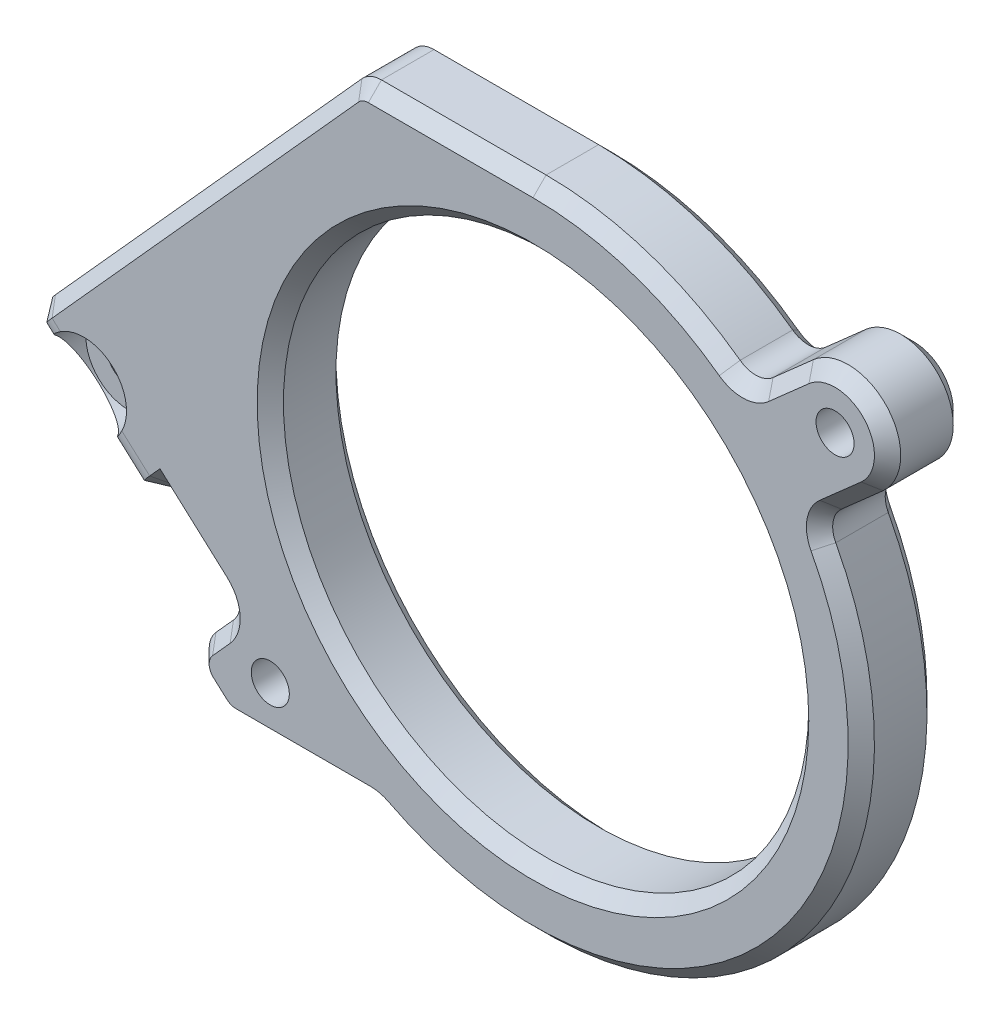
SolidWorks part; units mm, degrees
ref_plane "正面" through (0, 0, 0) normal (0, 0, 1) x (1, 0, 0)
ref_plane "平面" through (0, 0, 0) normal (0, 1, 0) x (1, 0, 0)
ref_plane "右側面" through (0, 0, 0) normal (1, 0, 0) x (0, 0, -1)
sketch "ｽｹｯﾁ1" plane through (0, 0, 0) normal (0, 0, 1) x (1, 0, 0)
  line L1 (30, -27.5) -> (-30, -27.5)
  line L2 (30, -27.5) -> (30, 27.5)
  line L3 (30, 27.5) -> (-30, 27.5)
  line L4 (-30, -27.5) -> (-30, 27.5)
  line L5 (30, -27.5) -> (-30, 27.5) construction
  line L6 (30, 27.5) -> (-30, -27.5) construction
  point P0 (0, 0)
  dimension "D1" = 55
  dimension "D2" = 60
extrude "ﾎﾞｽ - 押し出し1" add sketch "ｽｹｯﾁ1" along normal blind 6
sketch "ｽｹｯﾁ2" plane through (0, 0, 6) normal (0, 0, 1) x (1, 0, 0)
  line L0 (23, 20) -> (-20, -18)
  point P2 (0, 0)
  dimension "D1" = 18
  dimension "D2" = 20
  dimension "D3" = 43
  dimension "D4" = 38
hole_wizard "M4 すきま穴1" positions "ｽｹｯﾁ3" profile "ｽｹｯﾁ4" hole size "M4" standard "ISO"
sketch "ｽｹｯﾁ3" plane through (0, 0, 6) normal (0, 0, 1) x (1, 0, 0)
  point P0 (-20, -18)
  point P3 (23, 20)
sketch "ｽｹｯﾁ4" plane through (-20, -18, 6) normal (1, 0, 0) x (0, -1, 0)
  line L0 (0, 0) -> (0, 10)
  line L1 (0, 10) -> (1.45, 10)
  line L2 (1.45, 10) -> (1.45, 0)
  line L5 (1.45, 0) -> (0, 0)
  line L10 (0, 10) -> (-1.45, 10) construction
  line L11 (0, -6.35) -> (0, 107.95) construction
  dimension "穴の直径" = 2.9
  dimension "穴の深さ" = 10
  dimension "ﾄﾞﾘﾙ角度" = 180
sketch "ｽｹｯﾁ5" plane through (0, 0, 6) normal (0, 0, 1) x (1, 0, 0)
  circle A0 centre (0, 0) radius 20
  dimension "D1" = 40
extrude "ｶｯﾄ - 押し出し1" cut sketch "ｽｹｯﾁ5" against normal through all
sketch "ｽｹｯﾁ6" plane through (0, 0, 6) normal (0, 0, 1) x (1, 0, 0)
  line L0 (-20, -18) -> (23, 20) construction
  line L1 (23, 20) -> (-20, -18) construction
  line L2 (-22.6488, -15.0027) -> (20.3512, 22.9973)
  line L3 (-17.3512, -20.9973) -> (25.6488, 17.0027)
  line L8 (-30, 27.5) -> (-30, -27.5)
  line L9 (-30, -27.5) -> (30, -27.5)
  line L10 (30, -27.5) -> (30, 27.5)
  line L11 (30, 27.5) -> (-30, 27.5)
  line L12 (-30, 27.5) -> (-30, -27.5)
  line L13 (-30, -27.5) -> (30, -27.5)
  line L14 (30, -27.5) -> (30, 27.5)
  line L15 (30, 27.5) -> (-30, 27.5)
  circle A0 centre (0, 0) radius 20 construction
  circle A1 centre (0, 0) radius 20
  arc A2 (-22.6488, -15.0027) -> (-17.3512, -20.9973) centre (-20, -18) ccw
  arc A3 (25.6488, 17.0027) -> (20.3512, 22.9973) centre (23, 20) ccw
  circle A4 centre (0, 0) radius 25
  point P8 (1.5, 1)
  dimension "D2" = 50
  dimension "D1" = 8
  dimension "D3" = 0
extrude "ｶｯﾄ - 押し出し2" cut sketch "ｽｹｯﾁ6" against normal through all contours L13 L14 L15 L12 | A4 | A2 L3 A3 L2
sketch "ｽｹｯﾁ7" plane through (0, 0, 6) normal (0, 0, 1) x (1, 0, 0)
  line L0 (0, 25) -> (-20, 25)
  line L1 (-20, -22) -> (-21.5, -22)
  line L2 (-20, -22) -> (-20, 25)
  line L3 (-20, 25) -> (-21.5, 25)
  line L4 (-21.5, -22) -> (-21.5, 25)
  line L5 (-20, -22) -> (-11.8743, -22)
  line L8 (-21.0078, -13.5525) -> (-22.6488, -15.0027)
  line L9 (-17.3512, -20.9973) -> (-15.651, -19.4948)
  line L10 (21.2717, 13.1345) -> (25.6488, 17.0027)
  line L11 (20.3512, 22.9973) -> (16.0334, 19.1815)
  line L12 (-21.0078, -13.5525) -> (-22.6488, -15.0027)
  line L13 (-17.3512, -20.9973) -> (-15.651, -19.4948)
  line L14 (21.2717, 13.1345) -> (25.6488, 17.0027)
  line L15 (20.3512, 22.9973) -> (16.0334, 19.1815)
  arc A0 (-22.6488, -15.0027) -> (-17.3512, -20.9973) centre (-20, -18) ccw construction
  arc A5 (-22.6488, -15.0027) -> (-17.3512, -20.9973) centre (-20, -18) ccw
  arc A6 (-15.651, -19.4948) -> (21.2717, 13.1345) centre (0, 0) ccw
  arc A7 (25.6488, 17.0027) -> (20.3512, 22.9973) centre (23, 20) ccw
  arc A8 (16.0334, 19.1815) -> (-21.0078, -13.5525) centre (0, 0) ccw
  arc A9 (-22.6488, -15.0027) -> (-17.3512, -20.9973) centre (-20, -18) ccw
  arc A10 (-15.651, -19.4948) -> (21.2717, 13.1345) centre (0, 0) ccw
  arc A11 (25.6488, 17.0027) -> (20.3512, 22.9973) centre (23, 20) ccw
  arc A12 (16.0334, 19.1815) -> (-21.0078, -13.5525) centre (0, 0) ccw
  line M17 (-21.0078, -13.5525) -> (-22.6488, -15.0027)
  arc M18 (-22.6488, -15.0027) -> (-17.3512, -20.9973) centre (-20, -18) ccw
  line M19 (-17.3512, -20.9973) -> (-15.651, -19.4948)
  arc M20 (-15.651, -19.4948) -> (21.2717, 13.1345) centre (0, 0) ccw
  arc M24 (16.0334, 19.1815) -> (-21.0078, -13.5525) centre (0, 0) ccw
  dimension "D2" = 1.5
  dimension "D1" = 0
extrude "ﾎﾞｽ - 押し出し2" add sketch "ｽｹｯﾁ7" against normal up to surface (6 mm away) contours L4 L1 M18 M17 M24 | L4 L2 L3 M24 | L2 L0 M24 | L5 M18 M20 M19
sketch "ｽｹｯﾁ8" plane through (0, 0, 6) normal (0, 0, 1) x (1, 0, 0)
  line L0 (-21.5, 25) -> (-45.7174, -1.8961)
  line L1 (-45.7174, -1.8961) -> (-23.3898, -22)
  line L3 (-21.5, 12.7574) -> (-21.5, 25) construction
  line L4 (-20, -22) -> (-23.3898, -22)
  point P3 (-22.5, -21)
  point P9 (-21.5, -22)
  point P10 (0, 0)
  point P11 (0, 0)
  point P13 (0, 0)
  point P15 (-21.5, -22)
  point P16 (-24.0724, -22)
  point P17 (-21.5, 25)
  point P19 (0, 0)
  point P20 (-21.6569, -22)
  point P21 (0, 0)
  dimension "D1" = 42
  dimension "D2" = 32
extrude "ﾎﾞｽ - 押し出し3" add sketch "ｽｹｯﾁ8" against normal up to surface (6 mm away) up to face at (-3.845, 3.3122, 0)
sketch "ｽｹｯﾁ9" plane through (0, 0, 0) normal (0, 0, -1) x (-1, 0, 0)
  line L0 (32.3408, -13.9405) -> (25.6495, -6.509)
  line L1 (23.3898, -22) -> (45.7174, -1.8961) construction
  line L2 (25.6495, -6.509) -> (39.0261, 5.5353)
  line L3 (45.7174, -1.8961) -> (21.5, 25) construction
  line M4 (23.3898, -22) -> (45.7174, -1.8961)
  line M5 (45.7174, -1.8961) -> (21.5, 25)
  dimension "D1" = 10
  dimension "D2" = 18
extrude "ﾎﾞｽ - 押し出し4" add sketch "ｽｹｯﾁ9" along normal blind 4 contours L2 L0 M4 M5
sketch "ｽｹｯﾁ10" plane through (0, 0, -4) normal (0, 0, -1) x (-1, 0, 0)
  line L0 (32.3408, -13.9405) -> (25.6495, -6.509) construction
  line L1 (25.6495, -6.509) -> (39.0261, 5.5353) construction
  line L2 (39.0261, 5.5353) -> (21.5, 25) construction
  line L3 (21.5, 25) -> (0, 25) construction
  line L4 (-16.0334, 19.1815) -> (-20.3512, 22.9973) construction
  line L5 (-25.6488, 17.0027) -> (-21.2717, 13.1345) construction
  line L6 (11.8743, -22) -> (23.3898, -22) construction
  line L8 (39.0261, 5.5353) -> (25.6495, -6.509) construction
  line L9 (25.6495, -6.509) -> (32.3408, -13.9405) construction
  line L10 (32.3408, -13.9405) -> (45.7174, -1.8961) construction
  line L11 (45.7174, -1.8961) -> (39.0261, 5.5353) construction
  line L12 (32.3408, -13.9405) -> (25.6495, -6.509)
  line L13 (34.5672, 1.5205) -> (39.0261, 5.5353)
  line L14 (39.0261, 5.5353) -> (21.5, 25)
  line L15 (21.5, 25) -> (13.4262, 25)
  line L16 (-16.0334, 19.1815) -> (-20.3512, 22.9973)
  line L17 (-25.6488, 17.0027) -> (-21.2717, 13.1345)
  line L18 (11.8743, -22) -> (23.3898, -22)
  line L20 (39.0261, 5.5353) -> (34.5672, 1.5205)
  line L21 (25.6495, -6.509) -> (32.3408, -13.9405)
  line L22 (41.2585, -5.9109) -> (45.7174, -1.8961)
  line L23 (45.7174, -1.8961) -> (39.0261, 5.5353)
  line L24 (41.2585, -5.9109) -> (13.4262, 25)
  line L29 (39.0261, 5.5353) -> (25.6495, -6.509)
  line L30 (25.6495, -6.509) -> (32.3408, -13.9405)
  line L31 (32.3408, -13.9405) -> (45.7174, -1.8961)
  line L32 (45.7174, -1.8961) -> (39.0261, 5.5353)
  line L33 (39.0261, 5.5353) -> (34.5672, 1.5205)
  line L34 (25.6495, -6.509) -> (32.3408, -13.9405)
  line L35 (32.3408, -13.9405) -> (45.7174, -1.8961)
  line L36 (45.7174, -1.8961) -> (39.0261, 5.5353)
  arc A0 (0, 25) -> (-16.0334, 19.1815) centre (0, 0) ccw construction
  arc A1 (-20.3512, 22.9973) -> (-25.6488, 17.0027) centre (-23, 20) ccw construction
  arc A2 (-21.2717, 13.1345) -> (11.8743, -22) centre (0, 0) ccw construction
  arc A3 (0, 25) -> (-16.0334, 19.1815) centre (0, 0) ccw
  arc A4 (-20.3512, 22.9973) -> (-25.6488, 17.0027) centre (-23, 20) ccw
  arc A5 (-21.2717, 13.1345) -> (11.8743, -22) centre (0, 0) ccw
  dimension "D1" = 6
  dimension "D2" = 0
extrude "ｶｯﾄ - 押し出し3" cut sketch "ｽｹｯﾁ10" against normal through all contours L14 L15 L24 L22 L23
sketch "ｽｹｯﾁ12" plane through (0, 0, 6) normal (0, 0, 1) x (1, 0, 0)
  line L0 (-41.2585, -5.9109) -> (-26.4793, -19.2181)
  line L1 (-41.2585, -5.9109) -> (-37.2437, -1.452)
  line L2 (-26.4793, -19.2181) -> (-22.4646, -14.7593)
  line L3 (-37.2437, -1.452) -> (-22.4646, -14.7593)
  line L4 (-41.2585, -5.9109) -> (-23.3898, -22) construction
  circle A0 centre (-20, -18) radius 1.45 construction
  dimension "D1" = 4
  dimension "D2" = 6
extrude "ｶｯﾄ - 押し出し4" cut sketch "ｽｹｯﾁ12" against normal blind 6
fillet "ﾌｨﾚｯﾄ1" radius 2 3 edges at (-25.6495, -6.509, -2) (-34.5672, 1.5205, -2) (-26.4793, -19.2181, 3)
sketch "ｽｹｯﾁ13" plane through (0, 0, 0) normal (0, 0, 1) x (1, 0, 0)
  line L4 (-32.3408, -13.9405) -> (-28.326, -9.4816)
  line L5 (-28.326, -9.4816) -> (-37.2437, -1.452)
  line L6 (-37.2437, -1.452) -> (-41.2585, -5.9109)
  line L7 (-41.2585, -5.9109) -> (-32.3408, -13.9405)
  line L8 (-32.3408, -13.9405) -> (-28.326, -9.4816)
  line L9 (-28.326, -9.4816) -> (-37.2437, -1.452)
  line L10 (-37.2437, -1.452) -> (-41.2585, -5.9109)
  line L11 (-41.2585, -5.9109) -> (-32.3408, -13.9405)
  dimension "D1" = 0
extrude "ﾎﾞｽ - 押し出し5" add sketch "ｽｹｯﾁ13" along normal blind 6
chamfer "面取り2" distance 5 angle 45 1 edges at (-36.7996, -9.9257, 6)
fillet "ﾌｨﾚｯﾄ4" radius 2 8 edges at (-23.3898, -22, 3) (-13.4262, 25, 3) (-22.4646, -14.7593, 3) (-33.454, -6.21, 6) (-36.7996, -9.9257, 1) (21.2717, 13.1345, 3) (16.0334, 19.1815, 3) (-11.8743, -22, 3)
chamfer "面取り3" distance 1 angle 45 53 edges at (-29.6643, -10.9679, -4) (-32.3408, -13.9405, -1.9142) (-36.7996, -9.9257, -4) (-38.582, -2.9383, -4) (-30.1083, -2.4942, -4) (-34.5239, 0.6932, -4) (-26.4768, -6.5524, -4) (-24.472, -16.9887, 6) (-24.472, -16.9887, 0) (-24.4767, -21.0213, 6) (-25.6521, -19.1748, 6) (-25.6521, -19.1748, 0) (-24.4767, -21.0213, 0) (-25.6903, 11.3794, 6) (-28.3834, -9.5454, 6) (-26.1384, -11.4513, 6) (-17.4957, -22, 6) (17.8053, -17.5491, 6) (24.0713, 15.6086, 6) (18.8154, 21.6401, 6) (7.7717, 23.7613, 6) (-13.3492, 24.8271, 6) (-23.3388, -21.8672, 6) (-17.4957, -22, 0) (-26.1384, -11.4513, 0) (-24.9638, 12.1863, 0) (-6.2679, 25, 0) (7.7717, 23.7613, 0) (18.8154, 21.6401, 0) (24.0713, 15.6086, 0) (17.8053, -17.5491, 0) (-13.3492, 24.8271, 0) (-23.3388, -21.8672, 0) (-41.2585, -5.9109, -1.9142) (-39.5857, -4.0531, 3.5) (-37.8707, -2.1483, 5.8478) (-41.1566, -5.7978, 0.9369) (-30.668, -12.0826, 3.5) (-28.9529, -10.1779, 5.8478) (-32.2389, -13.8273, 0.9369) (21.8499, 13.0707, 0) (21.8499, 13.0707, 6) (16.0467, 19.7836, 0) (16.0467, 19.7836, 6) (-11.8979, -22.0563, 6) (-11.8979, -22.0563, 0) (-23.2919, -14.8026, 6) (-23.2919, -14.8026, 0) (20, 0, 0) (20, 0, 6) (25.9973, 22.6488, 0) (25.9973, 22.6488, 6) (-6.2679, 25, 6)
sketch "ｽｹｯﾁ14" plane through (0, 0, 6) normal (0, 0, 1) x (1, 0, 0)
  line L0 (-32.8997, -5.5943) -> (-34.1971, -5.5408)
  line L11 (-36.6154, -2.2487) -> (-29.1839, -8.94)
  line L21 (-36.6154, -2.2487) -> (-29.1839, -8.94)
  line L50 (-33.0839, -13.2714) -> (-40.5154, -6.58) construction
  line L87 (-13.2789, 23.6691) -> (-36.6154, -2.2487)
  line L88 (-13.2789, 23.6691) -> (-36.6154, -2.2487)
  line L89 (-29.1839, -8.94) -> (-28.4, -8.0693)
  line L90 (-29.1839, -8.94) -> (-28.4, -8.0693)
  line L97 (-22.622, -21) -> (-12.3693, -21)
  line L98 (-22.622, -21) -> (-12.3693, -21)
  line L99 (21.8316, 14.9639) -> (24.9866, 17.752)
  line L100 (21.8316, 14.9639) -> (24.9866, 17.752)
  line L101 (21.0134, 22.248) -> (17.9417, 19.5335)
  line L102 (21.0134, 22.248) -> (17.9417, 19.5335)
  line L103 (0, 24) -> (-12.5357, 24)
  line L104 (0, 24) -> (-12.5357, 24)
  line L115 (-40.3934, -4.9501) -> (-37.8317, -2.105) construction
  line L152 (-28.4, -8.0693) -> (-23.2817, -12.6779)
  line L153 (-28.4, -8.0693) -> (-23.2817, -12.6779)
  line L154 (-23.0597, -16.9147) -> (-24.3979, -18.401)
  line L155 (-23.0597, -16.9147) -> (-24.3979, -18.401)
  line L156 (-24.3239, -19.8133) -> (-23.2912, -20.7431)
  line L157 (-24.3239, -19.8133) -> (-23.2912, -20.7431)
  arc A94 (-12.5357, 24) -> (-13.2789, 23.6691) centre (-12.5357, 23) ccw
  arc A95 (-12.5357, 24) -> (-13.2789, 23.6691) centre (-12.5357, 23) ccw
  arc A100 (-10.9949, -21.3333) -> (-12.3693, -21) centre (-12.3693, -24) ccw
  arc A101 (-10.9949, -21.3333) -> (-12.3693, -21) centre (-12.3693, -24) ccw
  arc A102 (-10.9949, -21.3333) -> (21.1717, 11.303) centre (0, 0) ccw
  arc A103 (-10.9949, -21.3333) -> (21.1717, 11.303) centre (0, 0) ccw
  arc A104 (21.8316, 14.9639) -> (21.1717, 11.303) centre (23.8182, 12.7159) ccw
  arc A105 (21.8316, 14.9639) -> (21.1717, 11.303) centre (23.8182, 12.7159) ccw
  arc A106 (24.9866, 17.752) -> (21.0134, 22.248) centre (23, 20) ccw
  arc A107 (24.9866, 17.752) -> (21.0134, 22.248) centre (23, 20) ccw
  arc A108 (14.1824, 19.3613) -> (17.9417, 19.5335) centre (15.9552, 21.7815) ccw
  arc A109 (14.1824, 19.3613) -> (17.9417, 19.5335) centre (15.9552, 21.7815) ccw
  arc A110 (14.1824, 19.3613) -> (0, 24) centre (0, 0) ccw
  arc A111 (14.1824, 19.3613) -> (0, 24) centre (0, 0) ccw
  arc A157 (-23.0597, -16.9147) -> (-23.2817, -12.6779) centre (-25.2891, -14.9073) ccw
  arc A158 (-23.0597, -16.9147) -> (-23.2817, -12.6779) centre (-25.2891, -14.9073) ccw
  arc A159 (-24.3979, -18.401) -> (-24.3239, -19.8133) centre (-23.6548, -19.0701) ccw
  arc A160 (-24.3979, -18.401) -> (-24.3239, -19.8133) centre (-23.6548, -19.0701) ccw
  arc A161 (-23.2912, -20.7431) -> (-22.622, -21) centre (-22.622, -20) ccw
  arc A162 (-23.2912, -20.7431) -> (-22.622, -21) centre (-22.622, -20) ccw
  point P16 (0, 0)
  dimension "D2" = 5
  dimension "D3" = 5
  dimension "D1" = 0
hole_wizard "M3 六角穴付き頭ねじ用座ぐり穴2" positions "ｽｹｯﾁ19" profile "ｽｹｯﾁ20" counterbore size "M3" standard "ISO"
sketch "ｽｹｯﾁ19" plane through (0, 0, 6) normal (0, 0, 1) x (1, 0, 0)
  point P0 (-34.1971, -5.5408)
sketch "ｽｹｯﾁ20" plane through (-34.1971, -5.5408, 6) normal (1, 0, 0) x (0, -1, 0)
  line L0 (0, 0) -> (0, 10.9914)
  line L1 (0, 10.9914) -> (1.65, 10)
  line L2 (1.65, 10) -> (1.65, 3.4)
  line L3 (1.65, 3.4) -> (3.25, 3.4)
  line L4 (3.25, 3.4) -> (3.25, 0)
  line L5 (3.25, 0) -> (0, 0)
  line L10 (0, 10.9914) -> (-1.65, 10) construction
  line L11 (0, -6.35) -> (0, 107.95) construction
  dimension "穴の直径" = 3.3
  dimension "穴の深さ" = 10
  dimension "座ぐり穴の直径" = 6.5
  dimension "座ぐり穴の深さ" = 3.4
  dimension "ﾄﾞﾘﾙ角度" = 118
